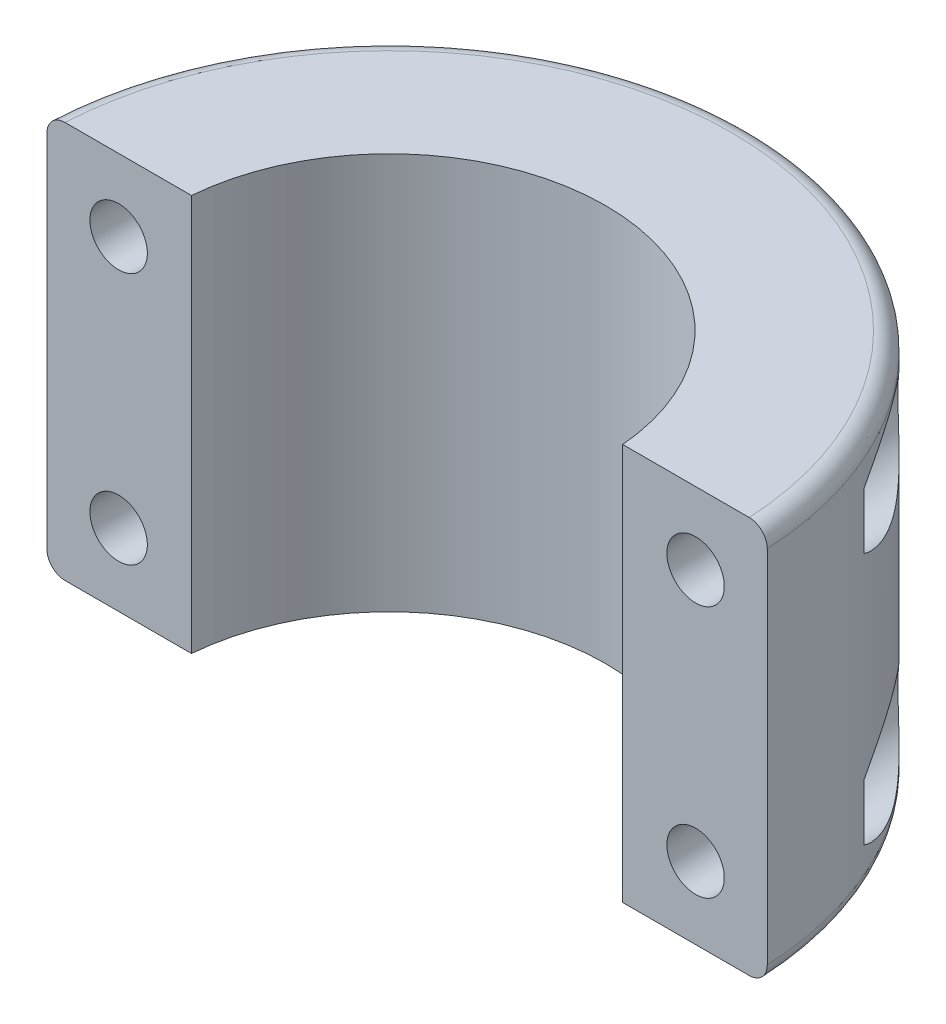
SolidWorks part; units mm, degrees
material "6061 Alloy"
ref_plane "Front Plane" through (0, 0, 0) normal (0, 0, 1) x (1, 0, 0)
ref_plane "Top Plane" through (0, 0, 0) normal (0, 1, 0) x (1, 0, 0)
ref_plane "Right Plane" through (0, 0, 0) normal (1, 0, 0) x (0, 0, -1)
sketch "Sketch1" plane through (0, 0, 0) normal (0, 1, 0) x (1, 0, 0)
  line L0 (-19.05, 0) -> (-31.75, 0)
  line L1 (19.05, 0) -> (31.75, 0)
  arc A0 (-31.75, 0) -> (31.75, 0) centre (0, 0) cw
  arc A1 (-19.05, 0) -> (19.05, 0) centre (0, 0) cw
  dimension "D1" = 19.05
  dimension "D2" = 31.75
extrude "Boss-Extrude1" add sketch "Sketch1" along normal blind 34.925
hole_wizard "#8 (0.199) Diameter Hole1" positions "Sketch3" profile "Sketch4" hole size "#8" standard "ANSI Inch" end condition through all
sketch "Sketch3" plane through (0, 0, 0) normal (0, 0, 1) x (1, 0, 0)
  line L0 (-31.75, 34.925) -> (-19.05, 34.925) construction
  line L1 (-31.75, 34.925) -> (-31.75, 0) construction
  point P0 (-25.4, 28.575)
  dimension "D1" = 6.35
  dimension "D2" = 6.35
sketch "Sketch4" plane through (-25.4, 28.575, 0) normal (1, 0, 0) x (0, -1, 0)
  line L0 (0, 0) -> (0, 31.75)
  line L1 (0, 31.75) -> (2.5273, 31.75)
  line L2 (2.5273, 31.75) -> (2.5273, 0)
  line L5 (2.5273, 0) -> (0, 0)
  line L11 (0, -6.35) -> (0, 107.95) construction
  dimension "Thru Hole Dia." = 5.0546
  dimension "Thru Hole Depth" = 31.75
pattern_linear "LPattern1" count 2 spacing 50.8 along (1, 0, 0) count 2 spacing 22.225 along (0, -1, 0) of "#8 (0.199) Diameter Hole1"
ref_plane "Plane1" through (0, 0, -31.75) normal (0, 0, -1) x (-1, 0, 0)
sketch "Sketch5" plane through (0, 0, -31.75) normal (0, 0, -1) x (-1, 0, 0)
  circle A0 centre (-25.4, 28.575) radius 4.445
  dimension "D1" = 8.89
extrude "Cut-Extrude1" cut sketch "Sketch5" against normal blind 19.05
pattern_linear "LPattern2" count 2 spacing 50.8 along (-1, 0, 0) count 2 spacing 22.225 along (0, -1, 0) of "Cut-Extrude1"
fillet "Fillet1" radius 1.5875 2 edges at (0, 0, -31.75) (0, 34.925, -31.75)
sketch "Sketch6" plane through (0, 0, 0) normal (0, 0, -1) x (-1, 0, 0)
  line L0 (-19.05, 34.925) -> (-30.1625, 34.925) construction
  line L1 (-31.75, 34.925) -> (31.855, 34.925)
  line L2 (-31.75, 34.925) -> (-31.75, -0.1304)
  line L3 (-31.75, -0.1304) -> (31.855, -0.1304)
  line L4 (31.855, 34.925) -> (31.855, -0.1304)
  line L5 (-31.75, 33.3375) -> (-31.75, 1.5875) construction
extrude "Cut-Extrude3" cut sketch "Sketch6" along normal blind 1.5875
